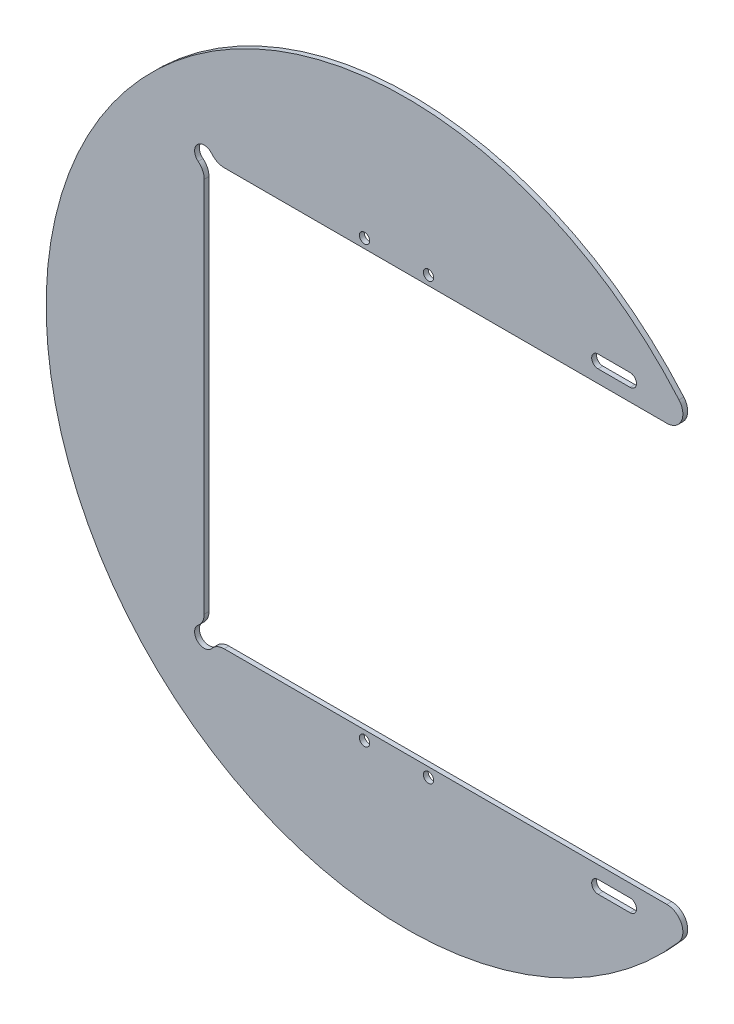
SolidWorks part; units mm, degrees
ref_plane "前视基准面" through (0, 0, 0) normal (0, 0, 1) x (1, 0, 0)
ref_plane "上视基准面" through (0, 0, 0) normal (0, 1, 0) x (1, 0, 0)
ref_plane "右视基准面" through (0, 0, 0) normal (1, 0, 0) x (0, 0, -1)
other "Configuration Table"
sketch "草图1" plane through (0, 0, 0) normal (0, 0, 1) x (1, 0, 0)
  circle A0 centre (0, 0) radius 112.5
  dimension "D1" = 225
extrude "凸台-拉伸1" add sketch "草图1" along normal blind 1.5
sketch "草图2" plane through (0, 0, 1.5) normal (0, 0, 1) x (1, 0, 0)
  line L0 (0, 0) -> (50000, 0) construction
  line L2 (-13, -68) -> (7, -68) construction
  line L3 (-13, -68) -> (-13, 68) construction
  line L4 (-13, 68) -> (7, 68) construction
  line L5 (7, -68) -> (7, 68) construction
  line L6 (-13, -68) -> (7, 68) construction
  line L7 (-13, 68) -> (7, -68) construction
  line L8 (112.5, -65.1) -> (-63.1, -65.1)
  line L9 (112.5, -65.1) -> (112.5, 65.1)
  line L10 (112.5, 65.1) -> (-63.1, 65.1)
  line L11 (-63.1, -65.1) -> (-63.1, 65.1)
  line L12 (112.5, -65.1) -> (-63.1, 65.1) construction
  line L13 (112.5, 65.1) -> (-63.1, -65.1) construction
  circle A0 centre (-13, 68) radius 1.6
  circle A1 centre (7, 68) radius 1.6
  circle A2 centre (-13, -68) radius 1.6
  circle A3 centre (7, -68) radius 1.6
  circle A4 centre (0, 0) radius 112.5 construction
  point P3 (-3, 0)
  point P12 (24.7, 0)
  dimension "D3" = 3.2
  dimension "D6" = 13
  dimension "D1" = 136
  dimension "D2" = 20
  dimension "D4" = 50.1
  dimension "D5" = 2.9
extrude "切除-拉伸1" cut sketch "草图2" against normal blind 10
fillet "圆角1" radius 5 2 edges at (91.751, -65.1, 0.75) (91.751, 65.1, 0.75)
sketch "草图3" plane through (0, 0, 1.5) normal (0, 0, 1) x (1, 0, 0)
  circle A0 centre (-63.1, 65.1) radius 3
  circle A1 centre (-63.1, -65.1) radius 3
  dimension "D1" = 6
extrude "切除-拉伸2" cut sketch "草图3" against normal blind 10
fillet "圆角2" radius 5 4 edges at (-60.1, -65.1, 0.75) (-63.1, -62.1, 0.75) (-60.1, 65.1, 0.75) (-63.1, 62.1, 0.75)
sketch "草图4" plane through (0, 0, 1.5) normal (0, 0, 1) x (1, 0, 0)
  line L0 (0, 71.1) -> (0, -71.1) construction
  line L1 (0, 71.1) -> (50000, 71.1) construction
  line L2 (0, -71.1) -> (50000, -71.1) construction
  line L3 (60, 71.1) -> (70, 71.1) construction
  line L4 (60, 73.1) -> (70, 73.1)
  line L5 (60, 69.1) -> (70, 69.1)
  line L6 (60, -71.1) -> (70, -71.1) construction
  line L7 (60, -69.1) -> (70, -69.1)
  line L8 (60, -73.1) -> (70, -73.1)
  line L9 (-56.855, -65.1) -> (81.4999, -65.1) construction
  line L10 (65, 71.1) -> (65, -71.1) construction
  arc A0 (60, 73.1) -> (60, 69.1) centre (60, 71.1) ccw
  arc A1 (70, 69.1) -> (70, 73.1) centre (70, 71.1) ccw
  arc A2 (60, -69.1) -> (60, -73.1) centre (60, -71.1) ccw
  arc A3 (70, -73.1) -> (70, -69.1) centre (70, -71.1) ccw
  point P4 (0, 0)
  point P10 (65, 71.1)
  point P16 (65, -71.1)
  dimension "D1" = 4
  dimension "D2" = 4
  dimension "D3" = 10
  dimension "D4" = 70
extrude "切除-拉伸3" cut sketch "草图4" against normal blind 10
